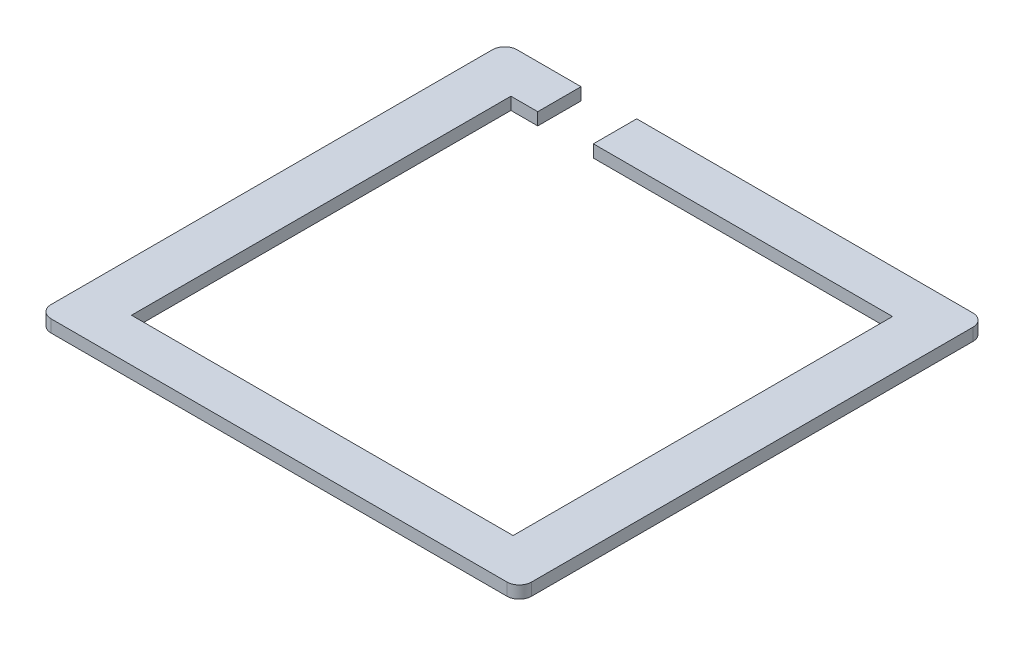
SolidWorks part; units mm, degrees
material "有机玻璃 (TM) GS 丙烯酸铸钣"
ref_plane "前视基准面" through (0, 0, 0) normal (0, 0, 1) x (1, 0, 0)
ref_plane "上视基准面" through (0, 0, 0) normal (0, 1, 0) x (1, 0, 0)
ref_plane "右视基准面" through (0, 0, 0) normal (1, 0, 0) x (0, 0, -1)
sketch "草图1" plane through (-113.3921, -3018.4732, -237.9473) normal (0, 1, 0) x (1, 0, 0)
  line L0 (-42.5289, -152.9249) -> (-118.2311, -152.9249) construction
  line L1 (-111.2311, -160.9249) -> (-49.5289, -160.9249)
  line L2 (-111.2311, -160.9249) -> (-111.2311, -222.2721)
  line L3 (-111.2311, -222.2721) -> (-49.5289, -222.2721)
  line L4 (-49.5289, -160.9249) -> (-49.5289, -222.2721)
  line L5 (-117.2311, -153.9249) -> (-43.5289, -153.9249)
  line L6 (-119.2311, -155.9249) -> (-119.2311, -227.2721)
  line L7 (-117.2311, -229.2721) -> (-43.5289, -229.2721)
  line L8 (-41.5289, -155.9249) -> (-41.5289, -227.2721)
  line L9 (-40.5289, -228.2721) -> (-40.5289, -154.9249) construction
  line L10 (-118.2311, -230.2721) -> (-42.5289, -230.2721) construction
  line L11 (-120.2311, -154.9249) -> (-120.2311, -228.2721) construction
  arc A0 (-43.5289, -153.9249) -> (-41.5289, -155.9249) centre (-43.5289, -155.9249) cw
  arc A1 (-41.5289, -227.2721) -> (-43.5289, -229.2721) centre (-43.5289, -227.2721) cw
  arc A2 (-117.2311, -229.2721) -> (-119.2311, -227.2721) centre (-117.2311, -227.2721) cw
  arc A3 (-119.2311, -155.9249) -> (-117.2311, -153.9249) centre (-117.2311, -155.9249) cw
  dimension "D5" = 2
  dimension "D1" = 1
  dimension "D2" = 1
  dimension "D3" = 1
  dimension "D4" = 1
extrude "凸台-拉伸1" add sketch "草图1" along normal blind 2
sketch "草图2" plane through (0, -3016.4732, 0) normal (0, 1, 0) x (1, 0, 0)
  line L0 (-156.921, 84.0225) -> (-230.6232, 84.0225) construction
  line L1 (-220.2841, 84.0225) -> (-211.2841, 84.0225)
  line L2 (-220.2841, 84.0225) -> (-220.2841, 77.0225)
  line L3 (-220.2841, 77.0225) -> (-211.2841, 77.0225)
  line L4 (-211.2841, 84.0225) -> (-211.2841, 77.0225)
  line L5 (-162.921, 77.0225) -> (-224.6232, 77.0225) construction
  line L6 (-224.6232, 77.0225) -> (-224.6232, 15.6752) construction
  dimension "D1" = 9
  dimension "D2" = 4.3391
extrude "切除-拉伸1" cut sketch "草图2" against normal blind 2
